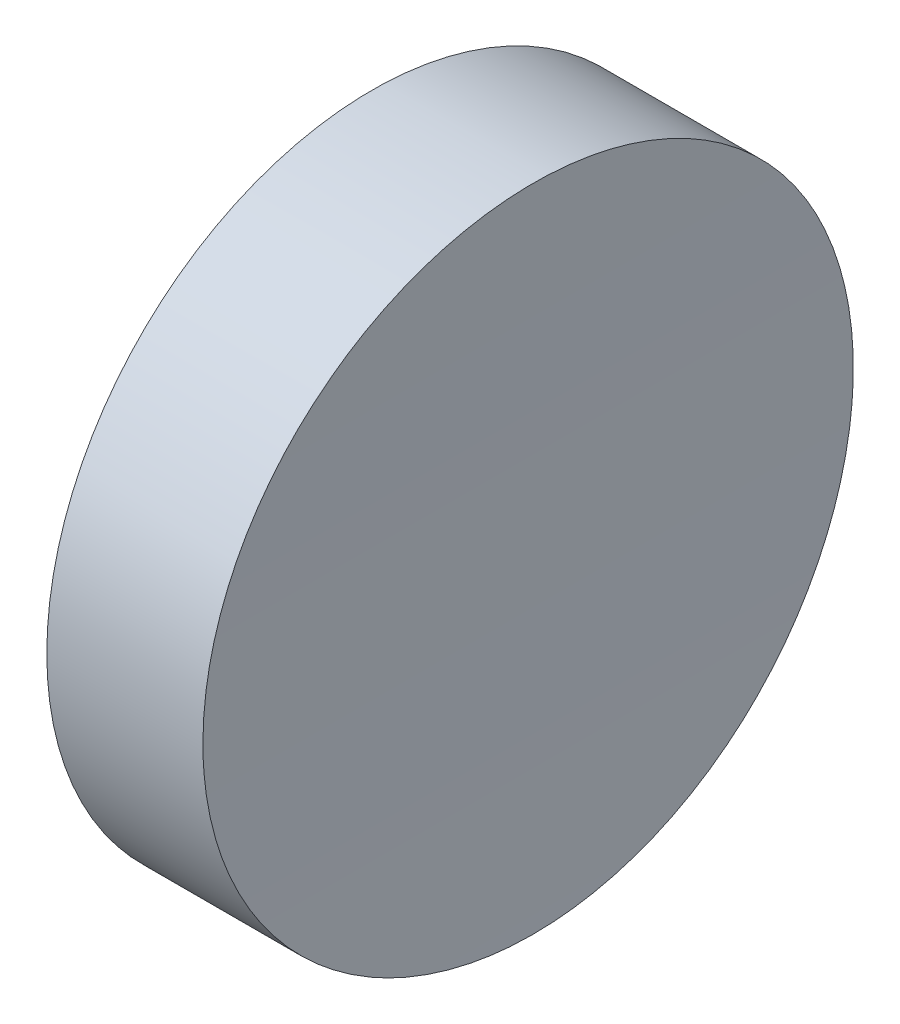
SolidWorks part; units mm, degrees
ref_plane "前视基准面" through (0, 0, 0) normal (0, 0, 1) x (1, 0, 0)
ref_plane "上视基准面" through (0, 0, 0) normal (0, 1, 0) x (1, 0, 0)
ref_plane "右视基准面" through (0, 0, 0) normal (1, 0, 0) x (0, 0, -1)
sketch "草图1" plane through (0, 0, 0) normal (1, 0, 0) x (0, 0, -1)
  circle A0 centre (0, 0) radius 12.5
  dimension "D1" = 25
extrude "凸台-拉伸1" add sketch "草图1" along normal blind 10
sketch "草图2" plane through (0, 0, 0) normal (0, 0, 1) x (1, 0, 0)
  line L0 (0, 0) -> (406, 0) construction
  line L1 (0, 0) -> (6, 0) construction
  circle A0 centre (406, 0) radius 400
  dimension "D1" = 800
  dimension "D2" = 6
extrude "切除-拉伸1" cut sketch "草图2" against normal through all both and the other way through all
